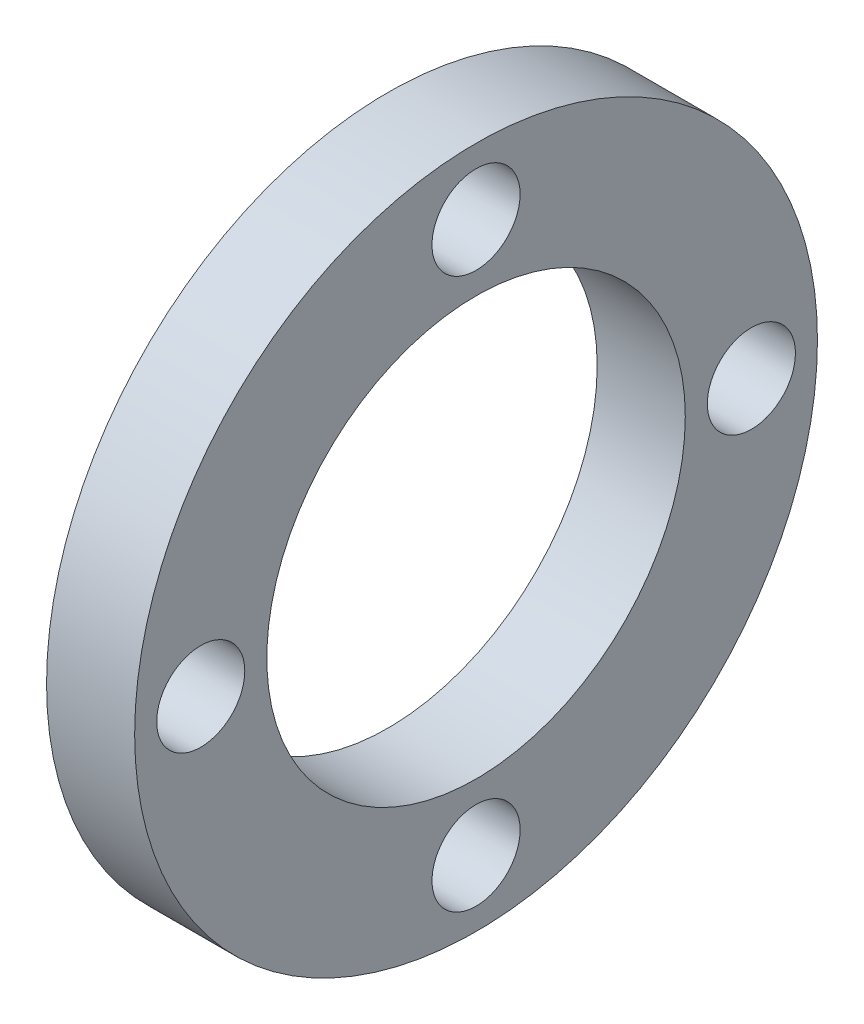
SolidWorks part; units mm, degrees
material "Acier non allié"
ref_plane "Plan de face" through (0, 0, 0) normal (0, 0, 1) x (1, 0, 0)
ref_plane "Plan de dessus" through (0, 0, 0) normal (0, 1, 0) x (1, 0, 0)
ref_plane "Plan de droite" through (0, 0, 0) normal (1, 0, 0) x (0, 0, -1)
sketch "Esquisse1" plane through (0, 0, 0) normal (1, 0, 0) x (0, 0, -1)
  circle A0 centre (0, 0) radius 31
  circle A1 centre (0, 0) radius 19
  circle A2 centre (0, 25) radius 4
  circle A3 centre (25, 0) radius 4
  circle A4 centre (0, -25) radius 4
  circle A5 centre (-25, 0) radius 4
  point P15 (0, 0)
  dimension "D1" = 38
  dimension "D2" = 62
  dimension "D3" = 25
  dimension "D4" = 4
extrude "Boss.-Extru.1" add sketch "Esquisse1" along normal blind 8
